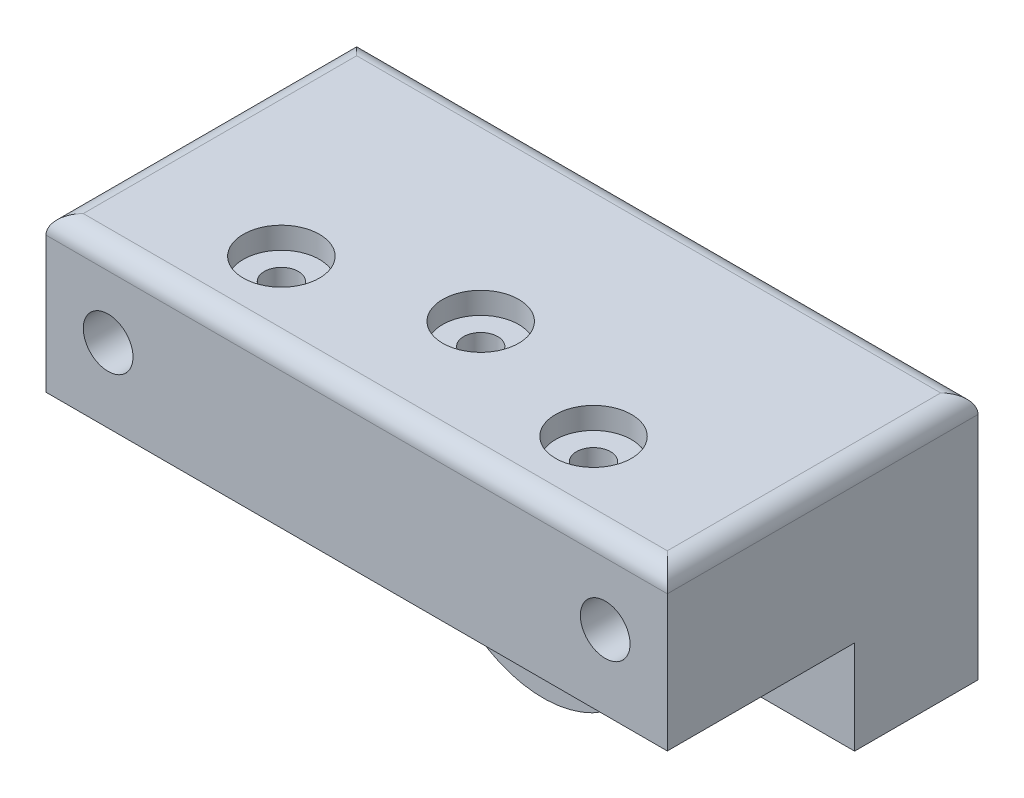
SolidWorks part; units mm, degrees
ref_plane "Plano frontal" through (0, 0, 0) normal (0, 0, 1) x (1, 0, 0)
ref_plane "Plano superior" through (0, 0, 0) normal (0, 1, 0) x (1, 0, 0)
ref_plane "Plano direito" through (0, 0, 0) normal (1, 0, 0) x (0, 0, -1)
sketch "Esboço1" plane through (0, 0, 127.8605) normal (0, 0, 1) x (1, 0, 0)
  line L0 (-54.2686, 0) -> (-54.2686, 30) construction
  line L1 (-564.3594, 15) -> (-54.2686, 15) construction
  line L2 (-564.3594, 30) -> (-564.3594, 0) construction
  line L5 (-309.314, 15) -> (-309.314, 30) construction
  line L6 (-359.314, 55) -> (-259.314, 55)
  line L7 (-359.314, 55) -> (-359.314, 15)
  line L8 (-359.314, 15) -> (-259.314, 15)
  line L9 (-259.314, 55) -> (-259.314, 15)
  line L10 (-534.314, 30) -> (-84.314, 30) construction
  line L11 (-309.314, 55) -> (-309.314, 15) construction
  circle A0 centre (-349.314, 42) radius 4
  circle A1 centre (-269.314, 42) radius 4
  dimension "D3" = 80
  dimension "D1" = 100
  dimension "D2" = 40
  dimension "D5" = 13
extrude "Ressalto-extrusão1" add sketch "Esboço1" against normal blind 50
fillet "Filete1" radius 3 4 edges at (-359.314, 55, 102.8605) (-309.314, 55, 77.8605) (-259.314, 55, 102.8605) (-309.314, 55, 127.8605)
sketch "Esboço3" plane through (-359.314, 0, 0) normal (-1, 0, 0) x (0, 0, 1)
  line L0 (127.8605, 52) -> (127.8605, 15) construction
  line L1 (127.8605, 30.0924) -> (97.7236, 30.0924)
  line L2 (127.8605, 30.0924) -> (127.8605, 15)
  line L3 (127.8605, 15) -> (97.7236, 15)
  line L4 (97.7236, 30.0924) -> (97.7236, 15)
extrude "Corte-extrusão1" cut sketch "Esboço3" against normal through all both and the other way through all
sketch "Esboço4" plane through (0, 0, 77.8605) normal (0, 0, -1) x (-1, 0, 0)
  line L0 (296.9956, 14.9758) -> (325.4335, 14.9758) construction
  line L1 (309.314, 29.7075) -> (309.314, -3.8169) construction
  circle A0 centre (309.314, 14.9758) radius 17.5
  dimension "D1" = 35
extrude "Ressalto-extrusão2" add sketch "Esboço4" against normal blind 20 and the other way blind 20
hole_wizard "Rebaixo para parafuso de cabeça sextavada de M51" positions "Esboço9" profile "Esboço10" size "M5" standard "ISO" slot yes end condition through all
sketch "Esboço9" plane through (0, 55, 0) normal (0, 1, 0) x (1, 0, 0)
  line L0 (-262.314, -124.8605) -> (-284.1953, -114.8605) construction
  line L1 (-284.1953, -114.8605) -> (-334.4327, -114.8605) construction
  line L2 (-334.4327, -114.8605) -> (-356.314, -124.8605) construction
  line L3 (-356.314, -80.8605) -> (-356.314, -124.8605) construction
  line L4 (-356.314, -124.8605) -> (-262.314, -124.8605) construction
  line L6 (-262.314, -124.8605) -> (-356.314, -124.8605) construction
  line L8 (-309.314, -124.8605) -> (-309.314, -80.8605) construction
  line L9 (-262.314, -80.8605) -> (-356.314, -80.8605) construction
  point P0 (-284.1953, -114.8605)
  point P2 (-334.4327, -114.8605)
  point P31 (-309.314, -107.8965)
  dimension "D1" = 10
sketch "Esboço10" plane through (-284.1953, 55, 114.8605) normal (1, 0, 0) x (0, 0, 1)
  line L0 (0, 0) -> (0, 57.5242)
  line L1 (0, 57.5242) -> (2.75, 57.5242)
  line L3 (2.75, 57.5242) -> (2.75, 3.5)
  line L4 (2.75, 3.5) -> (6.119, 3.5)
  line L5 (6.119, 3.5) -> (6.119, 0)
  line L7 (6.119, 0) -> (0, 0)
  line L11 (0, -6.35) -> (0, 107.95) construction
  dimension "Thru Hole Dia." = 5.5
  dimension "Thru Hole Depth" = 57.5242
  dimension "C'Bore Dia." = 12.238
  dimension "C'Bore Depth" = 3.5
